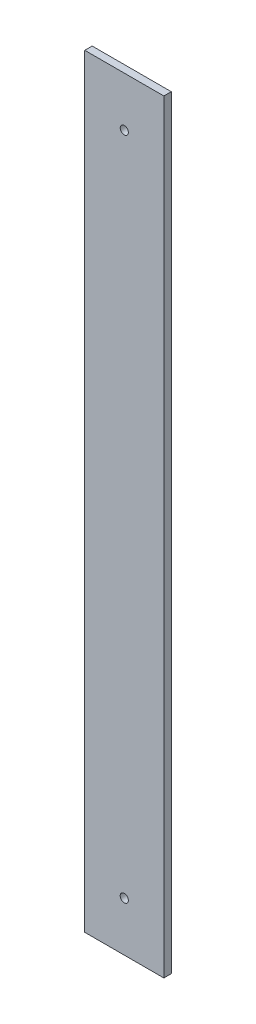
SolidWorks part; units mm, degrees
ref_plane "Plan de face" through (0, 0, 0) normal (0, 0, 1) x (1, 0, 0)
ref_plane "Plan de dessus" through (0, 0, 0) normal (0, 1, 0) x (1, 0, 0)
ref_plane "Plan de droite" through (0, 0, 0) normal (1, 0, 0) x (0, 0, -1)
sketch "Esquisse1" plane through (0, 0, 0) normal (0, 0, 1) x (1, 0, 0)
  line L1 (0, 0) -> (32, 0)
  line L2 (0, 0) -> (0, 309)
  line L3 (0, 309) -> (32, 309)
  line L4 (32, 0) -> (32, 309)
  dimension "D1" = 32
  dimension "D2" = 309
extrude "Boss.-Extru.1" add sketch "Esquisse1" along normal blind 3
sketch "Esquisse2" plane through (0, 0, 3) normal (0, 0, 1) x (1, 0, 0)
  line L0 (16, 309) -> (16, 289) construction
  line L1 (32, 309) -> (0, 309) construction
  line L2 (0, 154.5) -> (32, 154.5) construction
  line L3 (0, 309) -> (0, 0) construction
  line L4 (32, 0) -> (32, 309) construction
  circle A0 centre (16, 289) radius 1.65
  circle A1 centre (16, 20) radius 1.65
  dimension "D1" = 3.3
  dimension "D2" = 20
extrude "Enlèv. mat.-Extru.1" cut sketch "Esquisse2" against normal through all
